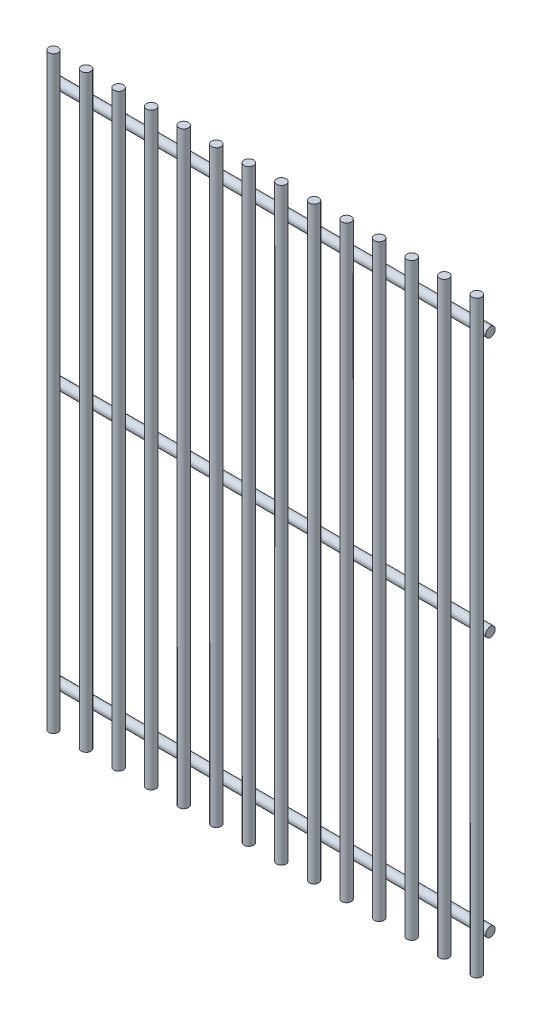
SolidWorks part; units mm, degrees
material "201 Annealed Stainless Steel (SS)"
ref_plane "Front Plane" through (0, 0, 0) normal (0, 0, 1) x (1, 0, 0)
ref_plane "Top Plane" through (0, 0, 0) normal (0, 1, 0) x (1, 0, 0)
ref_plane "Right Plane" through (0, 0, 0) normal (1, 0, 0) x (0, 0, -1)
sketch "Sketch1" plane through (0, 0, 0) normal (0, 1, 0) x (1, 0, 0)
  line L0 (-158.75, 0) -> (158.75, 0) construction
  line L1 (-158.75, 0) -> (-158.75, -10.4586) construction
  circle A0 centre (-155.25, -3.5) radius 3.5
  dimension "D2" = 7
  dimension "D1" = 317.5
extrude "Boss-Extrude1" add sketch "Sketch1" along normal mid plane 431.8
pattern_linear "LPattern1" count 14 spacing 23.8846 along (1, 0, 0) of bodies 101
sketch "Sketch2" plane through (0, 0, 0) normal (1, 0, 0) x (0, 0, -1)
  line L0 (0, 215.9) -> (-7, 215.9) construction
  line L1 (-7, -215.9) -> (0, -215.9) construction
  circle A0 centre (3, -190.5) radius 3.5
  circle A1 centre (3, 190.5) radius 3.5
  circle A2 centre (3, 0) radius 3.5
  dimension "D1" = 7
  dimension "D2" = 3
  dimension "D3" = 25.4
  dimension "D4" = 25.4
extrude "Boss-Extrude2" add sketch "Sketch2" along normal mid plane 317.5
equation "\"D3@LPattern1\"=(\"D1@Sketch1\"-(7mm))/13"
equation "\"D4@Sketch2\"=\"D3@Sketch2\""
